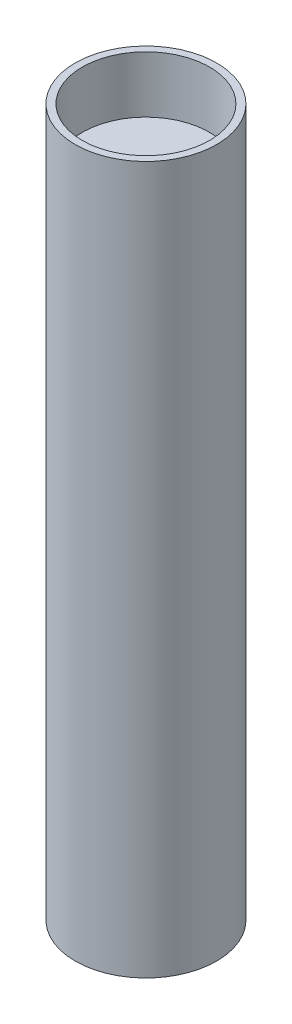
SolidWorks part; units mm, degrees
ref_plane "前视基准面" through (0, 0, 0) normal (0, 0, 1) x (1, 0, 0)
ref_plane "上视基准面" through (0, 0, 0) normal (0, 1, 0) x (1, 0, 0)
ref_plane "右视基准面" through (0, 0, 0) normal (1, 0, 0) x (0, 0, -1)
sketch "草图1" plane through (0, 0, 0) normal (0, 1, 0) x (1, 0, 0)
  circle A0 centre (0, 0) radius 10
  dimension "D1" = 20
extrude "凸台-拉伸1" add sketch "草图1" along normal blind 100
sketch "草图2" plane through (0, 100, 0) normal (0, 1, 0) x (1, 0, 0)
  circle A0 centre (0, 0) radius 9
  dimension "D1" = 18
extrude "切除-拉伸1" cut sketch "草图2" against normal blind 8
